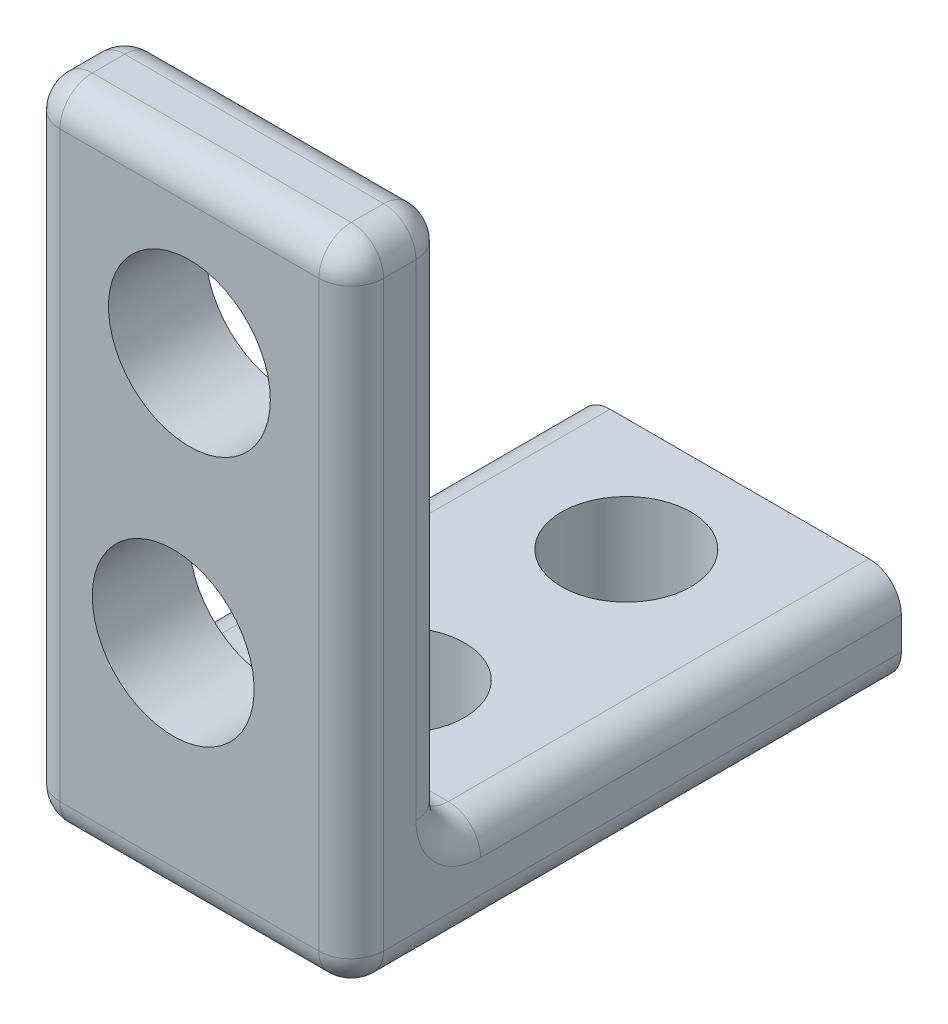
SolidWorks part; units mm, degrees
ref_plane "Front Plane" through (0, 0, 0) normal (0, 0, 1) x (1, 0, 0)
ref_plane "Top Plane" through (0, 0, 0) normal (0, 1, 0) x (1, 0, 0)
ref_plane "Right Plane" through (0, 0, 0) normal (1, 0, 0) x (0, 0, -1)
sketch "Sketch1" plane through (0, 0, 0) normal (0, 1, 0) x (1, 0, 0)
  line L1 (0, 0) -> (10, 0)
  line L2 (0, 0) -> (0, 20)
  line L3 (0, 20) -> (10, 20)
  line L4 (10, 0) -> (10, 20)
  dimension "D1" = 10
  dimension "D2" = 20
extrude "Boss-Extrude1" add sketch "Sketch1" along normal blind 20
sketch "Sketch2" plane through (0, 20, 0) normal (0, 1, 0) x (1, 0, 0)
  line L0 (0, 20) -> (0, 0) construction
  line L1 (0, 20) -> (10, 20)
  line L2 (0, 20) -> (0, 3)
  line L3 (0, 3) -> (10, 3)
  line L4 (10, 20) -> (10, 3)
  line L5 (10, 0) -> (10, 20) construction
  line L6 (10, 20) -> (0, 20) construction
  line L7 (0, 0) -> (10, 0) construction
  dimension "D1" = 0
  dimension "D2" = 3
extrude "Cut-Extrude1" cut sketch "Sketch2" against normal blind 17
sketch "Sketch3" plane through (0, 0, 0) normal (0, 0, 1) x (1, 0, 0)
  line L1 (10, 20) -> (10, 0) construction
  line L2 (0, 20) -> (10, 20) construction
  circle A0 centre (5, 15) radius 2.5
  dimension "D1" = 5
  dimension "D2" = 5
  dimension "D3" = 5
extrude "Cut-Extrude2" cut sketch "Sketch3" against normal through all
sketch "Sketch4" plane through (0, 3, 0) normal (0, 1, 0) x (1, 0, 0)
  line L0 (0, 20) -> (0, 3) construction
  line L1 (10, 20) -> (0, 20)
  line L2 (10, 20) -> (10, 17)
  line L3 (10, 17) -> (0, 17)
  line L4 (0, 20) -> (0, 17)
  dimension "D1" = 3
extrude "Cut-Extrude3" cut sketch "Sketch4" against normal through all
sketch "Sketch5" plane through (0, 3, 0) normal (0, 1, 0) x (1, 0, 0)
  line L0 (10, 3) -> (10, 17) construction
  line L1 (0, 17) -> (10, 17) construction
  line L2 (0, 3) -> (10, 3) construction
  circle A0 centre (5, 6.5) radius 2
  circle A1 centre (5, 13.5) radius 2
  dimension "D1" = 4
  dimension "D2" = 4
  dimension "D3" = 7
  dimension "D4" = 5
  dimension "D5" = 5
  dimension "D6" = 3.5
  dimension "D7" = 3.5
extrude "Cut-Extrude4" cut sketch "Sketch5" against normal through all
fillet "Fillet1" radius 1 14 edges at (5, 20, 0) (0, 20, -1.5) (5, 20, -3) (10, 20, -1.5) (5, 0, 0) (5, 3, -3) (10, 11.5, -3) (10, 0, -8.5) (10, 10, 0) (10, 3, -10) (0, 10, 0) (0, 0, -8.5) (0, 3, -10) (0, 11.5, -3)
sketch "Sketch6" plane through (0, 0, -3) normal (0, 0, -1) x (-1, 0, 0)
  line L2 (-9, 0) -> (-1, 0) construction
  line L3 (-10, 4) -> (-10, 19) construction
  circle A0 centre (-4.5, 7) radius 2.5
  dimension "D1" = 5
  dimension "D2" = 5.5
  dimension "D3" = 7
extrude "Cut-Extrude5" cut sketch "Sketch6" against normal through all
